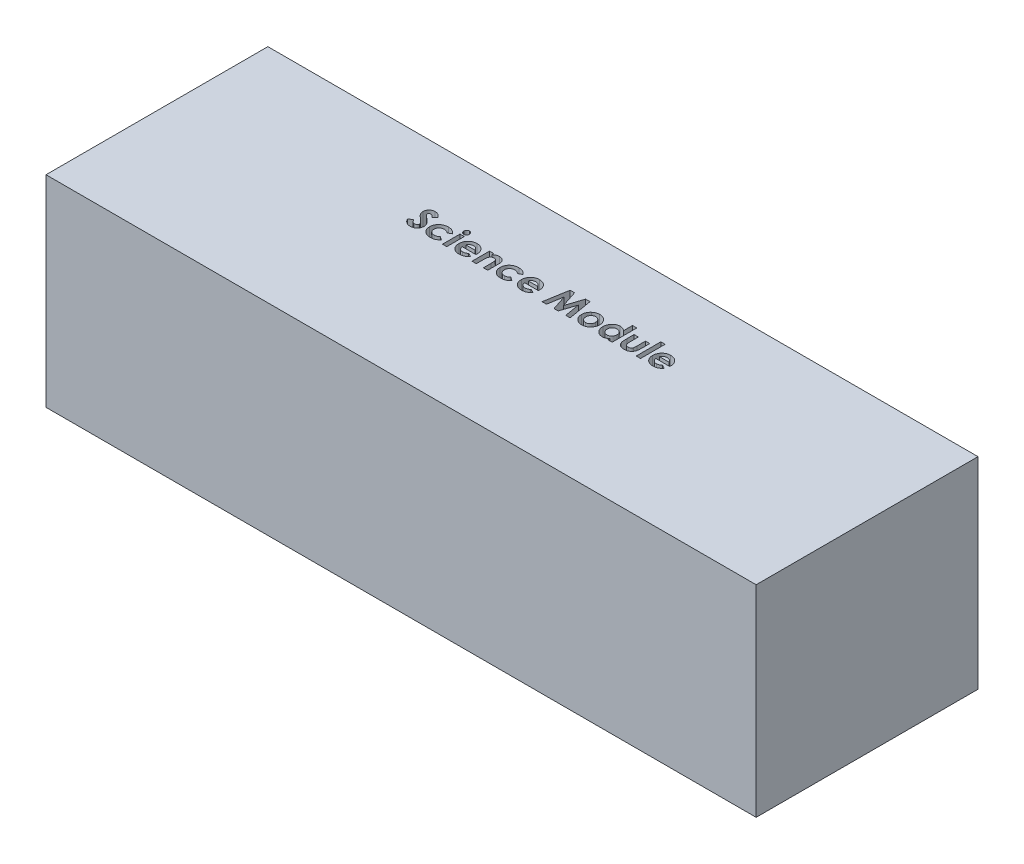
SolidWorks part; units mm, degrees
ref_plane "Front Plane" through (0, 0, 0) normal (0, 0, 1) x (1, 0, 0)
ref_plane "Top Plane" through (0, 0, 0) normal (0, 1, 0) x (1, 0, 0)
ref_plane "Right Plane" through (0, 0, 0) normal (1, 0, 0) x (0, 0, -1)
sketch "Sketch1" plane through (0, 0, 0) normal (0, 1, 0) x (1, 0, 0)
  line L1 (0, 0) -> (564, 0)
  line L2 (0, 0) -> (0, 176.2014)
  line L3 (0, 176.2014) -> (564, 176.2014)
  line L4 (564, 0) -> (564, 176.2014)
  dimension "D1" = 564
  dimension "D2" = 176.2014
extrude "Boss-Extrude1" add sketch "Sketch1" along normal blind 160
sketch "Sketch2" plane through (0, 160, 0) normal (0, 1, 0) x (1, 0, 0)
  line L0 (173.2077, 109.6768) -> (457.0401, 109.6768) construction
  text T0 "<b>Science Module</b>" font "Century Gothic" height in points 72
extrude "Cut-Extrude1" cut sketch "Sketch2" against normal blind 160
